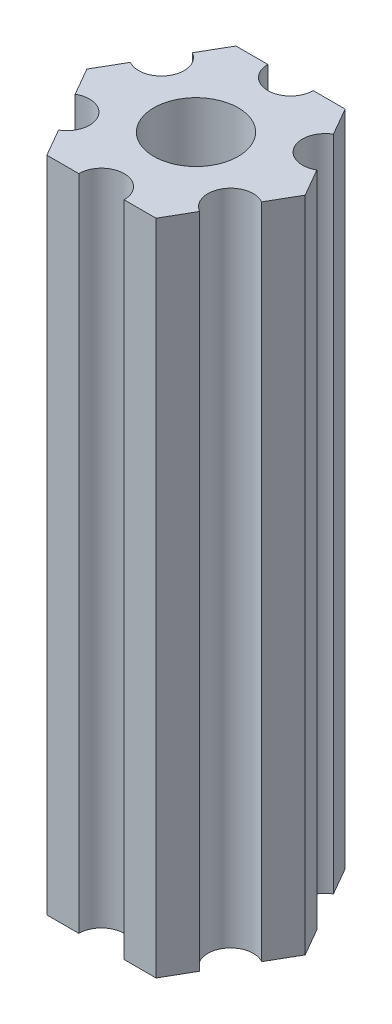
SolidWorks part; units mm, degrees
material "Churro - 6005A-T61"
ref_plane "Plano frontal" through (0, 0, 0) normal (0, 0, 1) x (1, 0, 0)
ref_plane "Plano superior" through (0, 0, 0) normal (0, 1, 0) x (1, 0, 0)
ref_plane "Plano direito" through (0, 0, 0) normal (1, 0, 0) x (0, 0, -1)
ref_plane "Plano1" through (0, 85, 0) normal (0, 1, 0) x (1, 0, 0)
sketch "Esboço1" plane through (0, 85, 0) normal (0, 1, 0) x (1, 0, 0)
  line L0 (6.1627, -1.826) -> (7.2169, 0)
  line L1 (7.2169, 0) -> (6.1627, 1.826)
  line L2 (4.6627, 4.424) -> (3.6084, 6.25)
  line L3 (3.6084, 6.25) -> (1.5, 6.25)
  line L4 (-1.5, 6.25) -> (-3.6084, 6.25)
  line L5 (-3.6084, 6.25) -> (-4.6627, 4.424)
  line L6 (-6.1627, 1.826) -> (-7.2169, 0)
  line L7 (-7.2169, 0) -> (-6.1627, -1.826)
  line L8 (-4.6627, -4.424) -> (-3.6084, -6.25)
  line L9 (-3.6084, -6.25) -> (-1.5, -6.25)
  line L10 (1.5, -6.25) -> (3.6084, -6.25)
  line L11 (3.6084, -6.25) -> (4.6627, -4.424)
  arc A0 (6.1627, 1.826) -> (4.6627, 4.424) centre (5.4127, 3.125) cw
  arc A1 (1.5, 6.25) -> (-1.5, 6.25) centre (0, 6.25) cw
  arc A2 (-4.6627, 4.424) -> (-6.1627, 1.826) centre (-5.4127, 3.125) cw
  arc A3 (-6.1627, -1.826) -> (-4.6627, -4.424) centre (-5.4127, -3.125) cw
  arc A4 (-1.5, -6.25) -> (1.5, -6.25) centre (0, -6.25) cw
  arc A5 (4.6627, -4.424) -> (6.1627, -1.826) centre (5.4127, -3.125) cw
  circle A6 centre (0, 0) radius 2.79
extrude "Ressalto-extrusão1" add sketch "Esboço1" against normal blind 43.5
